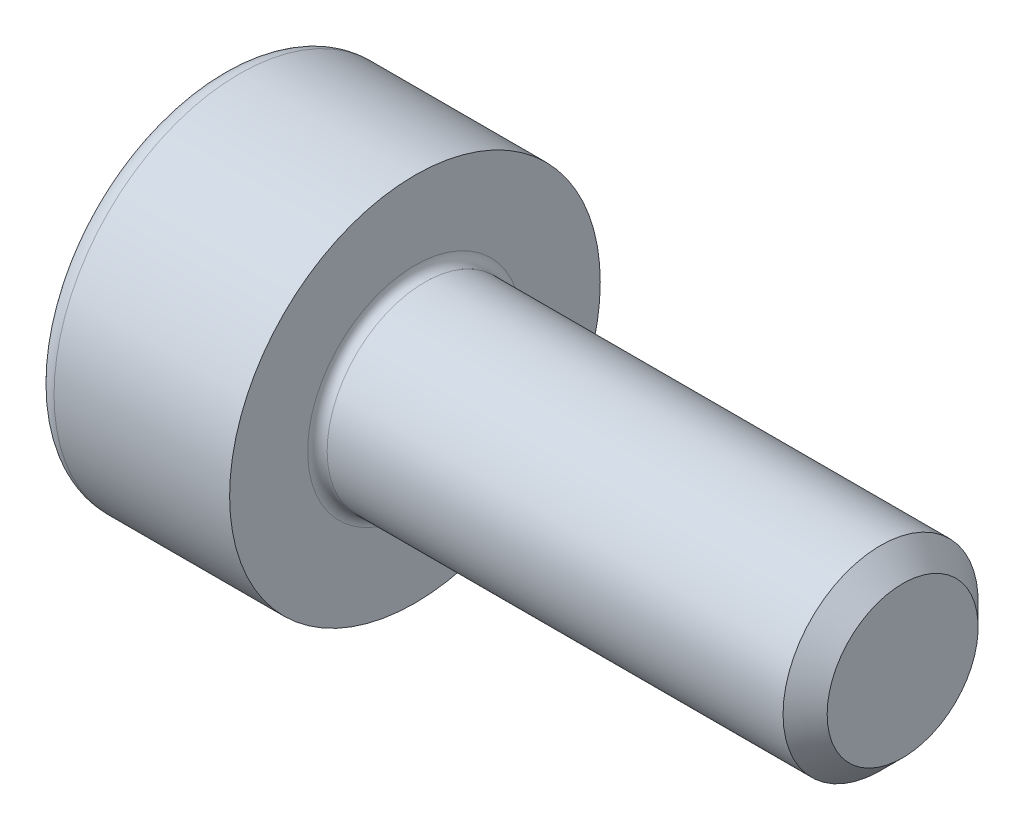
SolidWorks part; units mm, degrees
revolve "Base-Revolve" add sketch "BodySke"
sketch "BodySke" plane through (0, 0, 0) normal (0, 0, 1) x (1, 0, 0)
  line L0 (0, 0) -> (0, 1.9)
  line L1 (0, 1.9) -> (2, 1.9)
  line L2 (2, 1.9) -> (2, 1)
  line L3 (2, 1) -> (6.774, 1)
  line L4 (7, 0.774) -> (7, 0)
  line L5 (7, 0) -> (0, 0)
  line L6 (-31.75, 0) -> (127, 0) construction
  line L8 (7, 0.774) -> (6.774, 1)
  line L10 (7, -0.774) -> (6.774, -1) construction
  line L11 (2.4, 9.525) -> (2.4, 3.175) construction
  line L12 (2, 9.525) -> (2, 3.175) construction
  line L13 (-53, 9.525) -> (-53, 3.175) construction
  dimension "Head_ht" = 2
  dimension "Length" = 5
  dimension "Body_ch_ang" = 45
  dimension "Diameter" = 2
  dimension "Minor_dia" = 1.548
  dimension "Advance" = 0.4
  dimension "Thread_nom" = 5
  dimension "Thread_length" = 60
  dimension "Head_dia" = 3.8
cosmetic thread "ThreadCosmetic" [suppressed]
fillet "Fillet1" radius 0.1 1 edges at (2, 0, 1)
fillet "Fillet2" radius 0.2 1 edges at (0, 0, 1.9)
ref_plane "Plane1" through (0, 0, 0) normal (0, 0, 1) x (1, 0, 0)
ref_plane "Plane2" through (0, 0, 0) normal (0, 1, 0) x (1, 0, 0)
ref_plane "Plane3" through (0, 0, 0) normal (1, 0, 0) x (0, 0, -1)
sketch "Sketch2" plane through (0, 0, 0) normal (0, 0, 1) x (1, 0, 0)
  line L0 (0, 0.76) -> (1, 0.76)
  line L1 (1, 0.76) -> (1.4388, 0)
  line L2 (-31.75, 0) -> (127, 0) construction
  line L3 (1.4388, 0) -> (0, 0)
  line L4 (0, 0) -> (0, 0.76)
  line L6 (0, 0) -> (47.625, 0) construction
  dimension "D1" = 0.76
  dimension "D2" = 60
  dimension "Depth" = 1
revolve "Hex-PreBroach" cut sketch "Sketch2" angle 360 about L6
sketch "Sketch3" plane through (0, 0, 0) normal (-1, 0, 0) x (0, 0.5, 0.866)
  line L0 (0.4388, 0.76) -> (-0.4388, 0.76)
  line L1 (-0.4388, 0.76) -> (-0.8776, 0)
  line L2 (0.4388, 0.76) -> (0.8776, 0)
  line L3 (0.4388, -0.76) -> (0.8776, 0)
  line L4 (0.4388, -0.76) -> (-0.4388, -0.76)
  line L5 (-0.4388, -0.76) -> (-0.8776, 0)
  dimension "D1" = 0.76
  dimension "D2" = 0.76
  dimension "Hex_size" = 1.52
extrude "Hex" cut sketch "Sketch3" against normal blind 1
sketch "ThdSchSke" plane through (0, 0, 0) normal (0, 0, 1) x (1, 0, 0)
  line L0 (3.2, -0.774) -> (3.0418, -1)
  line L1 (3.2, -0.774) -> (3.3582, -1)
  line L2 (3.3582, -1) -> (3.3582, -1.25)
  line L3 (-3.175, 0) -> (5.1513, 0) construction
  line L4 (0, 1.7) -> (0, -1.7) construction
  line L5 (3.3582, -1.25) -> (3.0418, -1.25)
  line L6 (3.0418, -1.25) -> (3.0418, -1)
  dimension "Thread_minor" = 1.548
  dimension "Diameter" = 2
  dimension "Start" = 3.2
revolve "ThreadSchematic" [suppressed] cut sketch "ThdSchSke" angle 360 about L3
pattern_linear "ThdSchPat" [suppressed]
equation "\"D2@Sketch3\" = \"Hex_size@Sketch3\" / 2"
equation "\"D1@Sketch3\" = \"Hex_size@Sketch3\" / 2"
equation "\"D1@Sketch2\" = \"Hex_size@Sketch3\" / 2"
equation "\"Thread_minor@ThreadCosmetic\"  =  \"Minor_dia@BodySke\""
equation "\"Depth@Sketch2\" =  \"Key_eng@Hex\""
equation "\"Thread_length@ThreadCosmetic\" = ((sgn( (\"Length@BodySke\" - \"Advance@BodySke\" * 3.0) - \"Thread_nom@BodySke\" )-1)*( (\"Length@BodySke\" - \"Advance@BodySke\" * 3.0) - \"Thread_nom@BodySke\" ))/-2+ \"Thread_nom@BodySke\""
equation "\"Thread_minor@ThdSchSke\" = \"Minor_dia@BodySke\""
equation "\"Diameter@ThdSchSke\" = \"Diameter@BodySke\""
equation "\"Overcut@ThdSchSke\" = \"Diameter@BodySke\" * 1.25"
equation "\"Start@ThdSchSke\" = \"Head_ht@BodySke\" + \"Length@BodySke\" - \"Thread_length@ThreadCosmetic\"  '---Non-countersunk---"
equation "\"Num_threads@ThdSchPat\" = int( \"Thread_length@ThreadCosmetic\" / \"Advance@BodySke\" + 0.999 )  + 1"
equation "\"Advance@ThdSchPat\" = \"Thread_length@ThreadCosmetic\" /  (\"Num_threads@ThdSchPat\" - 1) 'relax it"
equation "\"Num_threads@ThdSchPat\" = \"Num_threads@ThdSchPat\" - sgn( \"Num_threads@ThdSchPat\" - 1) '---chamfered tips only---"
